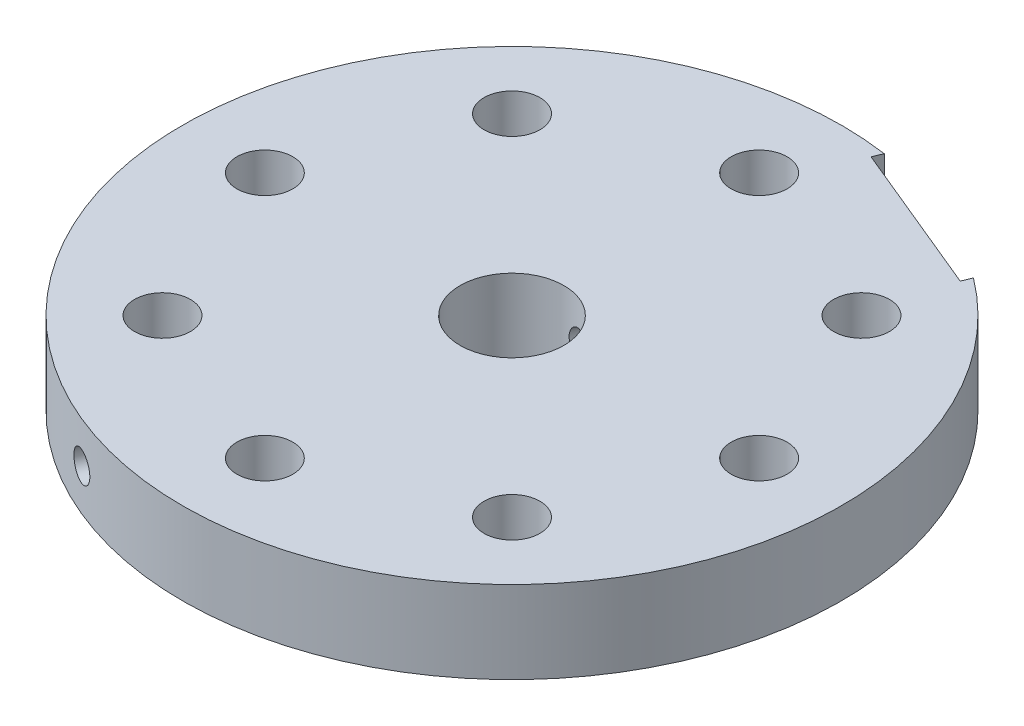
SolidWorks part; units mm, degrees
ref_plane "Front Plane" through (0, 0, 0) normal (0, 0, 1) x (1, 0, 0)
ref_plane "Top Plane" through (0, 0, 0) normal (0, 1, 0) x (1, 0, 0)
ref_plane "Right Plane" through (0, 0, 0) normal (1, 0, 0) x (0, 0, -1)
sketch "Sketch1" plane through (0, 0, 0) normal (0, 1, 0) x (1, 0, 0)
  circle A0 centre (0, 0) radius 25.4
  dimension "D1" = 50.8
extrude "Boss-Extrude1" add sketch "Sketch1" along normal blind 6.35
sketch "Sketch2" plane through (0, 6.35, 0) normal (0, 1, 0) x (1, 0, 0)
  circle A0 centre (0, 0) radius 6
  dimension "D1" = 12
extrude "Cut-Extrude1" [suppressed] cut sketch "Sketch2" against normal up to next
sketch "Sketch3" plane through (0, 6.35, 0) normal (0, 1, 0) x (1, 0, 0)
  line L0 (-24.2927, -24.2927) -> (24.2927, 24.2927) construction
  line L1 (22.0909, -22.0909) -> (-22.0909, 22.0909) construction
  line L2 (0, 0) -> (50.5386, 0) construction
  line L3 (0, 0) -> (0, 31.6562) construction
  circle A0 centre (0, 0) radius 19.05 construction
  circle A1 centre (-13.4704, 13.4704) radius 2.1527
  circle A2 centre (0, 19.05) radius 2.1526
  circle A3 centre (13.4704, 13.4704) radius 2.1526
  circle A4 centre (19.05, 0) radius 2.1527
  circle A5 centre (13.4704, -13.4704) radius 2.1526
  circle A6 centre (0, -19.05) radius 2.1526
  circle A7 centre (-13.4704, -13.4704) radius 2.1527
  circle A8 centre (-19.05, 0) radius 2.1527
  point P6 (0, 0)
  point P8 (0, 0)
  dimension "D1" = 38.1
  dimension "D2" = 4.3053
  dimension "D3" = 45
  dimension "D4" = 45
extrude "Cut-Extrude2" cut sketch "Sketch3" against normal up to next
sketch "Sketch4" plane through (0, 6.35, 0) normal (0, 1, 0) x (1, 0, 0)
  line L0 (0, 0) -> (9.7202, 23.4665)
  line L1 (0, 0) -> (57.6495, 0) construction
  dimension "D1" = 67.5
  dimension "D2" = 25.4
ref_plane "Plane1" through (9.7202, 0, -23.4665) normal (0.3827, 0, -0.9239) x (-0.9239, 0, -0.3827)
sketch "Sketch5" plane through (9.7202, 0, -23.4665) normal (0.3827, 0, -0.9239) x (-0.9239, 0, -0.3827)
  line L0 (6.35, 0) -> (-6.35, 0)
  line L1 (6.35, 0) -> (6.35, 6.35)
  line L2 (6.35, 6.35) -> (-6.35, 6.35)
  line L3 (-6.35, 6.35) -> (-6.35, 0)
  point P4 (0, 0)
  dimension "D1" = 12.7
  dimension "D2" = 6.35
extrude "Cut-Extrude3" cut sketch "Sketch5" against normal blind 1.5875
sketch "Sketch6" plane through (9.1126, 0, -21.9999) normal (0.3827, 0, -0.9239) x (-0.9239, 0, -0.3827)
  line L0 (0, 0) -> (0, 6.35) construction
  line L1 (-6.35, 0) -> (6.35, 0) construction
  circle A0 centre (0, 3.175) radius 1.1303
  dimension "D2" = 2.2606
  dimension "D1" = 6.35
extrude "4-40TappedHole" cut sketch "Sketch6" against normal up to next
sketch "Sketch7" [suppressed] plane through (9.1126, 0, -21.9999) normal (0.3827, 0, -0.9239) x (-0.9239, 0, -0.3827)
  line L0 (0, 0) -> (0, 6.35) construction
  line L1 (-6.35, 0) -> (6.35, 0) construction
  circle A0 centre (0, 3.175) radius 1.3526
  dimension "D2" = 2.7051
  dimension "D1" = 6.35
extrude "Cut-Extrude4" [suppressed] cut sketch "Sketch7" against normal up to next
sketch "Sketch8" plane through (0, 6.35, 0) normal (0, 1, 0) x (1, 0, 0)
  circle A0 centre (0, 0) radius 4
  dimension "D1" = 8
extrude "Cut-Extrude5" cut sketch "Sketch8" against normal up to next
